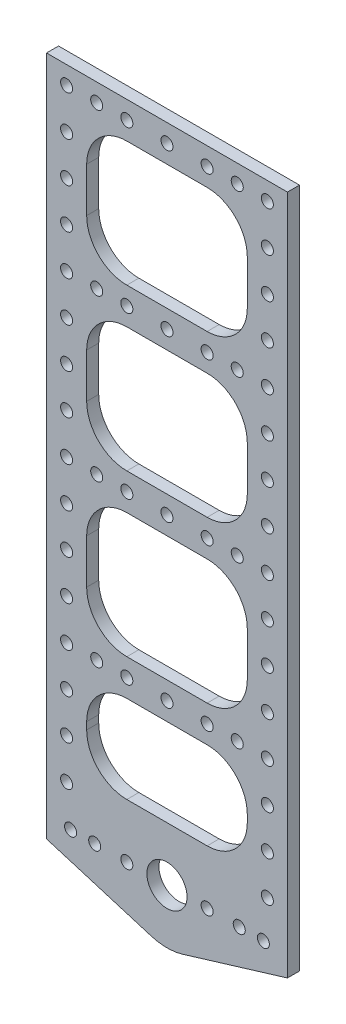
SolidWorks part; units mm, degrees
ref_plane "Front Plane" through (0, 0, 0) normal (0, 0, 1) x (1, 0, 0)
ref_plane "Top Plane" through (0, 0, 0) normal (0, 1, 0) x (1, 0, 0)
ref_plane "Right Plane" through (0, 0, 0) normal (1, 0, 0) x (0, 0, -1)
sketch "Sketch1" plane through (0, 0, 0) normal (0, 0, 1) x (1, 0, 0)
  line L0 (-29.5465, 1.7862) -> (-29.5465, 166.2862)
  line L1 (-29.5465, 166.2862) -> (30.4535, 166.2862)
  line L2 (30.4535, 166.2862) -> (30.4535, 1.7862)
  line L3 (0.4535, 15.2862) -> (-19.5465, 15.2862)
  line L4 (0.4535, 15.2862) -> (0.4535, -11.7138)
  line L5 (-29.5465, -16.7138) -> (30.4535, -16.7138)
  line L6 (-29.5465, -16.7138) -> (-29.5465, -0.5195)
  line L7 (0.4535, -16.7138) -> (0.4535, 1.7862)
  line L8 (30.4535, -16.7138) -> (30.4535, -0.5195)
  line L9 (30.4535, 1.7862) -> (-29.5465, 1.7862)
  line L10 (-29.5465, -3.2138) -> (-29.5465, 6.7862)
  line L13 (30.4535, -3.2138) -> (30.4535, 6.7862)
  line L14 (30.4535, -3.2138) -> (4.3755, -11.1316)
  line L15 (-29.5465, -3.2138) -> (-3.4686, -11.1316)
  line L16 (0.4535, 1.7862) -> (-9.5465, 1.7862)
  line L17 (-29.5465, 1.7862) -> (-23.5465, 1.7862)
  line L18 (-23.5465, 1.7862) -> (-17.5465, 1.7862)
  line L19 (-19.5465, 15.2862) -> (-19.5465, 157.2862)
  line L20 (-19.5465, 157.2862) -> (20.4535, 157.2862)
  line L21 (20.4535, 157.2862) -> (20.4535, 15.2862)
  line L22 (20.4535, 15.2862) -> (0.4535, 15.2862)
  line L23 (20.4535, 15.2862) -> (20.4535, 27.7862)
  line L24 (30.4535, 166.2862) -> (22.9535, 166.2862)
  line L25 (0.4535, 15.2862) -> (0.4535, 148.3544)
  line L26 (30.4535, 1.7862) -> (30.4535, 41.7862)
  line L27 (30.4535, 41.7862) -> (30.4535, 84.0362)
  line L28 (30.4535, 84.0362) -> (30.4535, 121.7862)
  line L29 (30.4535, 121.7862) -> (30.4535, 161.7862)
  line L30 (30.4535, 161.7862) -> (-29.5465, 161.7862)
  line L31 (0.4535, 15.2862) -> (0.4535, 166.2862)
  line L32 (30.4535, 161.7862) -> (25.4535, 161.7862)
  line L33 (-29.5465, 161.7862) -> (30.4535, 161.7862)
  line L34 (-19.5465, 157.2862) -> (20.4535, 157.2862)
  line L35 (-19.5465, 117.2179) -> (20.4535, 117.2179)
  line L36 (-19.5465, 126.2179) -> (20.4535, 126.2179)
  line L37 (-19.5465, 77.1497) -> (20.4535, 77.1497)
  line L38 (-19.5465, 86.1497) -> (20.4535, 86.1497)
  line L39 (-19.5465, 37.0815) -> (20.4535, 37.0815)
  line L40 (-19.5465, 46.0815) -> (20.4535, 46.0815)
  line L41 (-29.5465, 161.7862) -> (-24.5465, 161.7862)
  line L42 (-29.5465, 121.7862) -> (-29.5465, 161.7862)
  line L43 (-29.5465, 84.0362) -> (-29.5465, 121.7862)
  line L44 (-29.5465, 41.7862) -> (-29.5465, 84.0362)
  line L45 (-29.5465, 1.7862) -> (-29.5465, 41.7862)
  line L46 (-19.5465, 157.2862) -> (-19.5465, 15.2862)
  line L47 (20.4535, 15.2862) -> (20.4535, 157.2862)
  line L48 (-29.5465, 166.2862) -> (-29.5465, 1.7862)
  line L49 (30.4535, 1.7862) -> (30.4535, 166.2862)
  line L50 (22.9535, 166.2862) -> (26.7035, 166.2862)
  line L52 (20.4535, 157.2862) -> (30.4535, 157.2862)
  line L53 (30.4535, 157.2862) -> (25.4535, 157.2862)
  arc A0 (-3.4686, -11.1316) -> (4.3755, -11.1316) centre (0.4535, 1.7862) ccw
  circle A1 centre (-9.5465, 1.7862) radius 1.5
  circle A2 centre (-23.5465, 1.7862) radius 1.5
  circle A3 centre (-17.5465, 1.7862) radius 1.5
  circle A4 centre (10.4535, 1.7862) radius 1.5
  circle A5 centre (18.4535, 1.7862) radius 1.5
  circle A6 centre (24.4535, 1.7862) radius 1.5
  circle A7 centre (0.4535, 1.7862) radius 5
  circle A8 centre (25.4535, 161.7862) radius 1.5
  circle A9 centre (17.9535, 161.7862) radius 1.5
  circle A10 centre (10.4535, 161.7862) radius 1.5
  circle A11 centre (0.4535, 161.7862) radius 1.5
  circle A12 centre (0.4535, 121.7179) radius 1.5
  circle A13 centre (10.4535, 121.7179) radius 1.5
  circle A14 centre (17.9535, 121.7179) radius 1.5
  circle A15 centre (25.4535, 121.7179) radius 1.5
  circle A16 centre (0.4535, 81.6497) radius 1.5
  circle A17 centre (10.4535, 81.6497) radius 1.5
  circle A18 centre (17.9535, 81.6497) radius 1.5
  circle A19 centre (25.4535, 81.6497) radius 1.5
  circle A20 centre (0.4535, 41.5815) radius 1.5
  circle A21 centre (10.4535, 41.5815) radius 1.5
  circle A22 centre (17.9535, 41.5815) radius 1.5
  circle A23 centre (25.4535, 41.5815) radius 1.5
  circle A24 centre (-24.5465, 41.5815) radius 1.5
  circle A25 centre (-17.0465, 41.5815) radius 1.5
  circle A26 centre (-9.5465, 41.5815) radius 1.5
  circle A27 centre (-24.5465, 81.6497) radius 1.5
  circle A28 centre (-17.0465, 81.6497) radius 1.5
  circle A29 centre (-9.5465, 81.6497) radius 1.5
  circle A30 centre (-24.5465, 121.7179) radius 1.5
  circle A31 centre (-17.0465, 121.7179) radius 1.5
  circle A32 centre (-9.5465, 121.7179) radius 1.5
  circle A33 centre (-9.5465, 161.7862) radius 1.5
  circle A34 centre (-17.0465, 161.7862) radius 1.5
  circle A35 centre (-24.5465, 161.7862) radius 1.5
  circle A36 centre (25.4535, 151.7862) radius 1.5
  circle A37 centre (25.4535, 111.7179) radius 1.5
  circle A38 centre (25.4535, 71.6497) radius 1.5
  circle A39 centre (25.4535, 31.5815) radius 1.5
  circle A40 centre (-24.5465, 151.7862) radius 1.5
  circle A41 centre (-24.5465, 111.7179) radius 1.5
  circle A42 centre (-24.5465, 71.6497) radius 1.5
  circle A43 centre (-24.5465, 31.5815) radius 1.5
  circle A44 centre (25.4535, 141.7862) radius 1.5
  circle A45 centre (25.4535, 101.7179) radius 1.5
  circle A46 centre (25.4535, 61.6497) radius 1.5
  circle A47 centre (25.4535, 21.5815) radius 1.5
  circle A48 centre (-24.5465, 141.7862) radius 1.5
  circle A49 centre (-24.5465, 101.7179) radius 1.5
  circle A50 centre (-24.5465, 61.6497) radius 1.5
  circle A51 centre (-24.5465, 21.5815) radius 1.5
  circle A52 centre (25.4535, 131.7862) radius 1.5
  circle A53 centre (25.4535, 91.7179) radius 1.5
  circle A54 centre (25.4535, 51.6497) radius 1.5
  circle A55 centre (25.4535, 11.5815) radius 1.5
  circle A56 centre (-24.5465, 131.7862) radius 1.5
  circle A57 centre (-24.5465, 91.7179) radius 1.5
  circle A58 centre (-24.5465, 51.6497) radius 1.5
  circle A59 centre (-24.5465, 11.5815) radius 1.5
  point P116 (0.4535, 157.2862)
  dimension "D2" = 3
  dimension "D3" = 10
  dimension "D8" = 10
  dimension "D10" = 3
  dimension "D14" = 4
  dimension "D1" = 5
  dimension "D4" = 8
  dimension "D5" = 6
  dimension "D6" = 60
  dimension "D7" = 27
  dimension "D9" = 160
  dimension "D11" = 5
  dimension "D12" = 4.5
  dimension "D13" = 4.5
  dimension "D15" = 10
  dimension "D16" = 4
extrude "Boss-Extrude1" add sketch "Sketch1" along normal blind 3
fillet "Fillet1" radius 10 16 edges at (20.4535, 157.2862, 1.5) (-19.5465, 157.2862, 1.5) (-19.5465, 126.2179, 1.5) (20.4535, 126.2179, 1.5) (-19.5465, 37.0815, 1.5) (-19.5465, 15.2862, 1.5) (20.4535, 15.2862, 1.5) (20.4535, 37.0815, 1.5) (-19.5465, 77.1497, 1.5) (-19.5465, 46.0815, 1.5) (20.4535, 46.0815, 1.5) (20.4535, 77.1497, 1.5) (-19.5465, 117.2179, 1.5) (-19.5465, 86.1497, 1.5) (20.4535, 86.1497, 1.5) (20.4535, 117.2179, 1.5)
